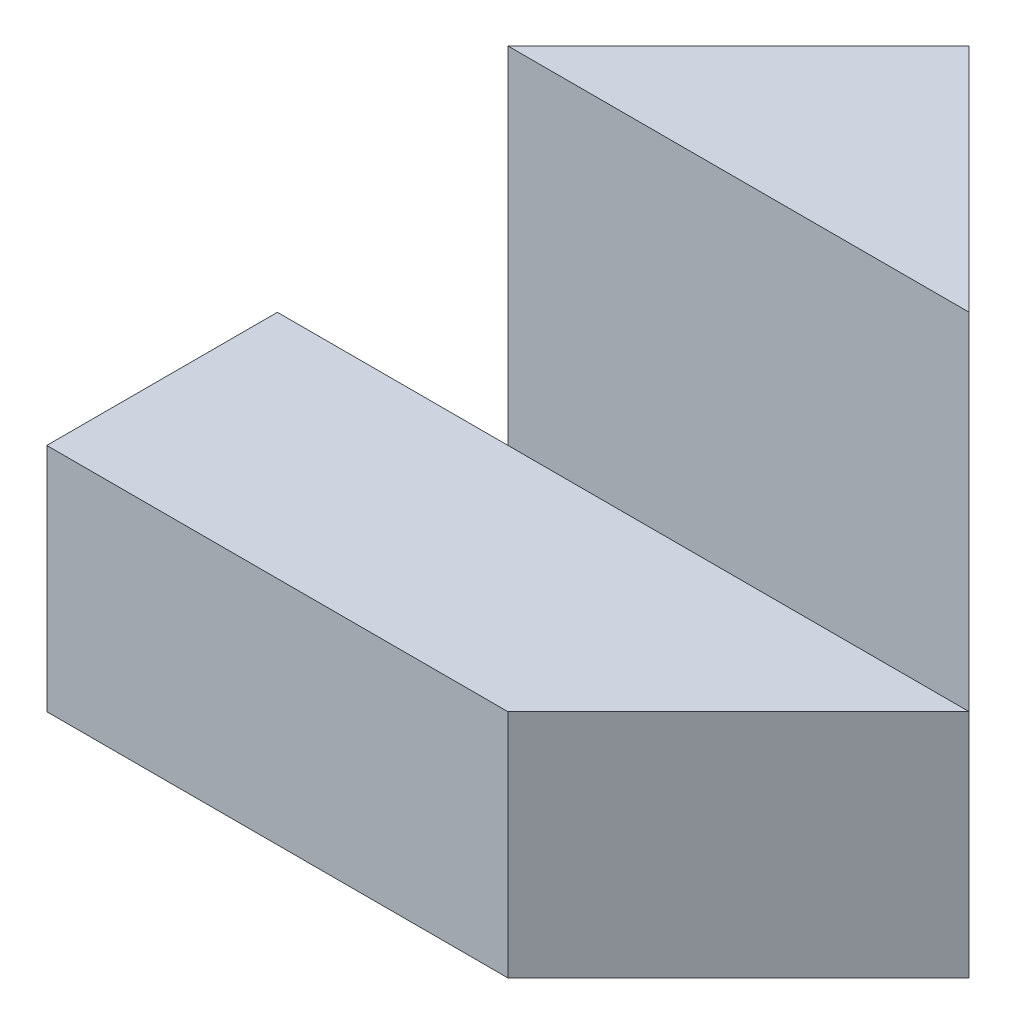
SolidWorks part; units mm, degrees
ref_plane "Front Plane" through (0, 0, 0) normal (0, 0, 1) x (1, 0, 0)
ref_plane "Top Plane" through (0, 0, 0) normal (0, 1, 0) x (1, 0, 0)
ref_plane "Right Plane" through (0, 0, 0) normal (1, 0, 0) x (0, 0, -1)
sketch "Sketch1" plane through (0, 0, 0) normal (0, 0, 1) x (1, 0, 0)
  line L1 (-2, -2.5) -> (2, -2.5)
  line L2 (-2, -2.5) -> (-2, 2.5)
  line L3 (-2, 2.5) -> (2, 2.5)
  line L4 (2, -2.5) -> (2, 2.5)
  line L5 (-2, -2.5) -> (2, 2.5) construction
  line L6 (-2, 2.5) -> (2, -2.5) construction
  point P0 (0, 0)
  dimension "D1" = 5
  dimension "D2" = 4
extrude "Boss-Extrude1" add sketch "Sketch1" along normal blind 2
sketch "Sketch2" plane through (0, 0, 2) normal (0, 0, 1) x (1, 0, 0)
  line L0 (2, -2.5) -> (2, 2.5) construction
  line L1 (-2, -2.5) -> (2, -2.5)
  line L2 (-2, -2.5) -> (-2, -0.5)
  line L3 (-2, -0.5) -> (2, -0.5)
  line L4 (2, -2.5) -> (2, -0.5)
  dimension "D1" = 2
extrude "Boss-Extrude2" add sketch "Sketch2" along normal blind 2
sketch "Sketch3" plane through (0, -0.5, 0) normal (0, 1, 0) x (1, 0, 0)
  line L0 (2, -4) -> (4, -2)
  line L1 (4, -2) -> (2, -2)
  line L2 (2, -2) -> (2, -4)
  dimension "D1" = 2
extrude "Boss-Extrude3" add sketch "Sketch3" against normal blind 2
sketch "Sketch4" plane through (0, 2.5, 0) normal (0, 1, 0) x (1, 0, 0)
  line L0 (2, 0) -> (4, -2)
  line L1 (4, -2) -> (1.3533, -2)
  line L2 (2, -2) -> (-2, -2) construction
  line L3 (1.3533, -2) -> (2, 0)
extrude "Boss-Extrude4" add sketch "Sketch4" against normal blind 5
sketch "Sketch5" plane through (0, 2.5, 0) normal (0, 1, 0) x (1, 0, 0)
  line L0 (-2, -2) -> (0, -2)
  line L1 (4, -2) -> (-2, -2) construction
  line L2 (0, -2) -> (2, 0)
  line L3 (2, 0) -> (-2, 0) construction
  line L4 (2, 0) -> (-2, 0)
  line L5 (-2, 0) -> (-2, -2)
  dimension "D1" = 4
extrude "Cut-Extrude1" cut sketch "Sketch5" against normal blind 5
